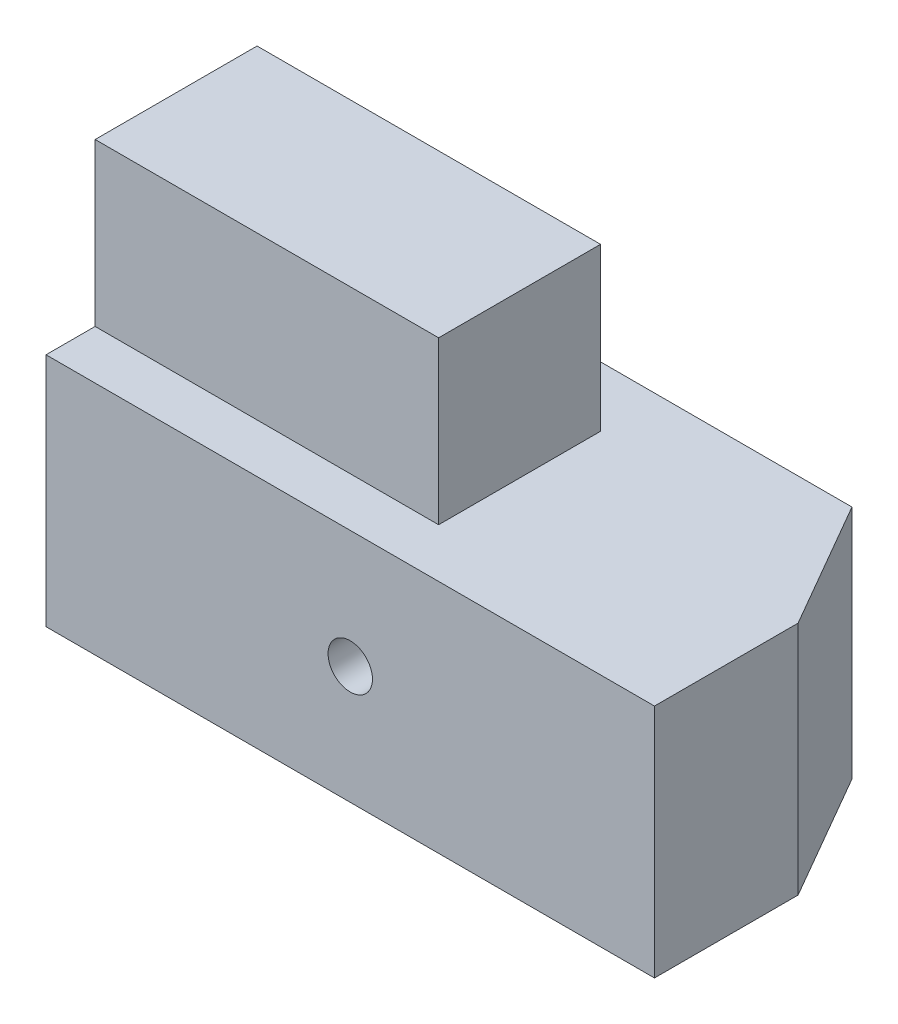
SolidWorks part; units mm, degrees
ref_plane "Front Plane" through (0, 0, 0) normal (0, 0, 1) x (1, 0, 0)
ref_plane "Top Plane" through (0, 0, 0) normal (0, 1, 0) x (1, 0, 0)
ref_plane "Right Plane" through (0, 0, 0) normal (1, 0, 0) x (0, 0, -1)
sketch "Sketch1" plane through (0, 0, 0) normal (0, 0, 1) x (1, 0, 0)
  line L0 (-62, 0) -> (62, 0) construction
  line L1 (-62, 24) -> (62, 24)
  line L2 (-62, 24) -> (-62, -24)
  line L3 (-62, -24) -> (62, -24)
  line L4 (62, 24) -> (62, -24)
  circle A0 centre (0, 0) radius 4.525
  dimension "D1" = 9.05
  dimension "D2" = 62
  dimension "D3" = 62
  dimension "D4" = 48
extrude "Boss-Extrude1" add sketch "Sketch1" against normal blind 55.25
sketch "Sketch2" plane through (0, 24, 0) normal (0, 1, 0) x (1, 0, 0)
  line L0 (62, 0) -> (-62, 0) construction
  line L1 (-61.99, 43) -> (8.01, 43)
  line L2 (-61.99, 43) -> (-61.99, 10)
  line L3 (-61.99, 10) -> (8.01, 10)
  line L4 (8.01, 43) -> (8.01, 10)
  line L5 (-62, 55.25) -> (-62, 0) construction
  dimension "D1" = 70
  dimension "D2" = 33
  dimension "D3" = 10
  dimension "D4" = 0.01
extrude "Boss-Extrude2" add sketch "Sketch2" along normal blind 33
chamfer "Chamfer1" distance 15 angle 60 1 edges at (62, 0, -55.25)
